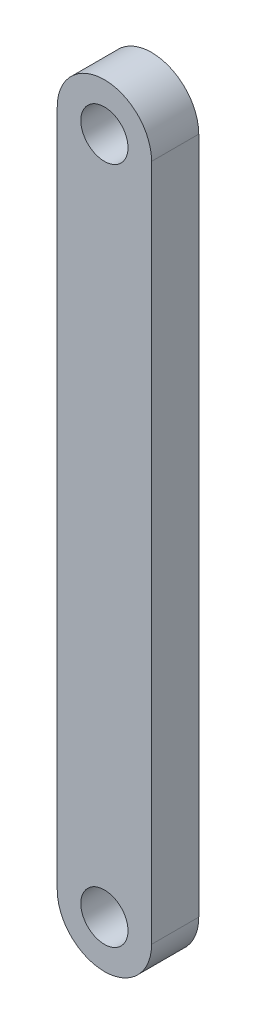
SolidWorks part; units mm, degrees
ref_plane "Front Plane" through (0, 0, 0) normal (0, 0, 1) x (1, 0, 0)
ref_plane "Top Plane" through (0, 0, 0) normal (0, 1, 0) x (1, 0, 0)
ref_plane "Right Plane" through (0, 0, 0) normal (1, 0, 0) x (0, 0, -1)
sketch "Sketch1" plane through (0, 0, 0) normal (0, 0, 1) x (1, 0, 0)
  line L0 (0, 0) -> (0, 115)
  line L1 (16, 0) -> (16, 115)
  arc A0 (16, 115) -> (0, 115) centre (8, 115) ccw
  arc A1 (0, 0) -> (16, 0) centre (8, 0) ccw
  point P9 (0, 0)
  point P10 (0, 0)
  dimension "D1" = 16
  dimension "D2" = 115
extrude "Boss-Extrude1" add sketch "Sketch1" along normal mid plane 8
sketch "Sketch2" plane through (0, 0, 4) normal (0, 0, 1) x (1, 0, 0)
  line L0 (0, 115) -> (16, 115) construction
  line L1 (0, 0) -> (50000, 0) construction
  circle A0 centre (8, 115) radius 4
  circle A1 centre (8, 0) radius 4
  arc A2 (0, 0) -> (16, 0) centre (8, 0) ccw construction
  arc A3 (16, 115) -> (0, 115) centre (8, 115) ccw construction
  point P12 (0, 0)
  point P16 (0, 0)
  dimension "D1" = 8
  dimension "D2" = 8
extrude "Cut-Extrude1" cut sketch "Sketch2" against normal through all
